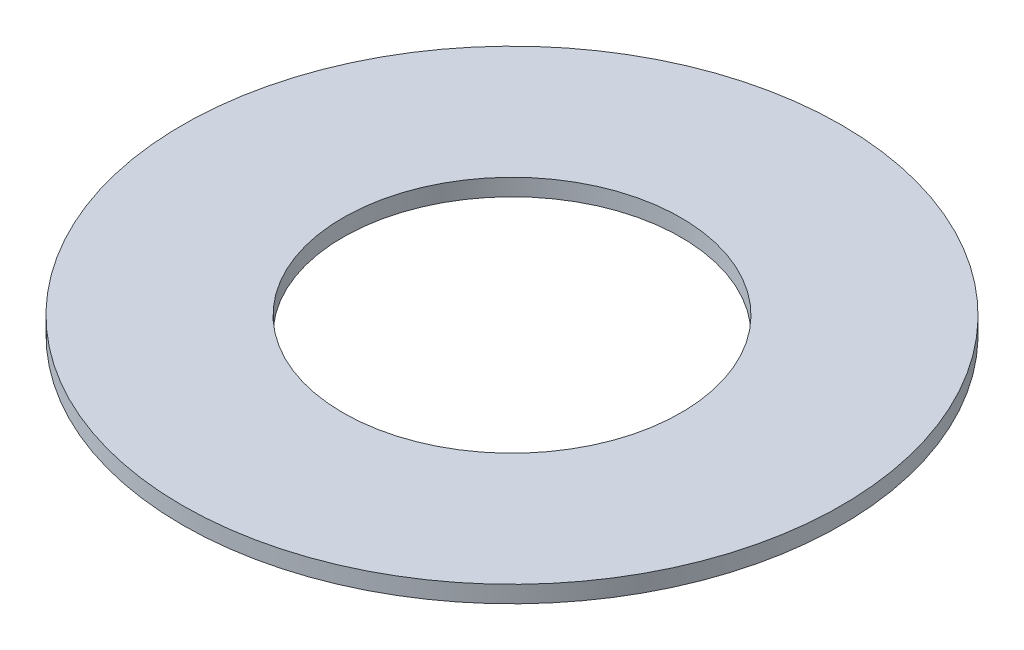
SolidWorks part; units mm, degrees
ref_plane "Front" through (0, 0, 0) normal (0, 0, 1) x (1, 0, 0)
ref_plane "Top" through (0, 0, 0) normal (0, 1, 0) x (1, 0, 0)
ref_plane "Right" through (0, 0, 0) normal (1, 0, 0) x (0, 0, -1)
sketch "Sketch1" plane through (0, 0, 0) normal (0, 1, 0) x (1, 0, 0)
  circle A0 centre (0, 0) radius 9.75
  circle A1 centre (0, 0) radius 5
  dimension "D1" = 19.5
  dimension "D2" = 10
extrude "Boss-Extrude1" add sketch "Sketch1" along normal blind 0.5
